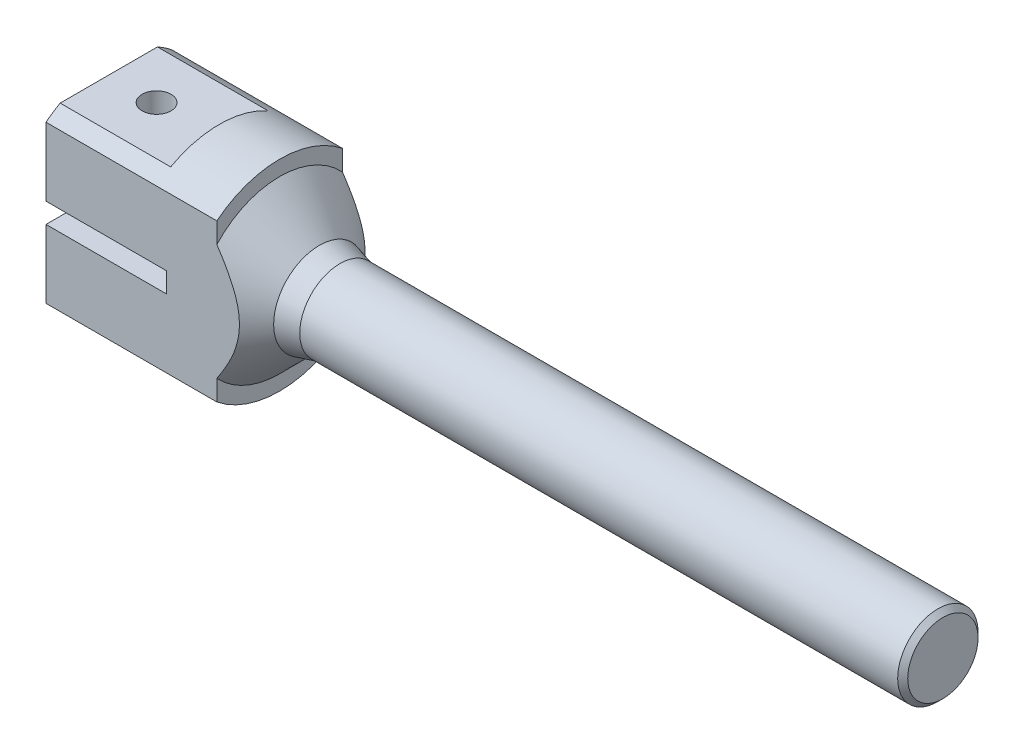
SolidWorks part; units mm, degrees
ref_plane "Ebene vorne" through (0, 0, 0) normal (0, 0, 1) x (1, 0, 0)
ref_plane "Ebene oben" through (0, 0, 0) normal (0, 1, 0) x (1, 0, 0)
ref_plane "Ebene rechts" through (0, 0, 0) normal (1, 0, 0) x (0, 0, -1)
sketch "Skizze1" plane through (0, 0, 0) normal (0, 0, 1) x (1, 0, 0)
  line L0 (0, 0) -> (0, 8)
  line L1 (-166, 20) -> (-132, 20)
  line L2 (0, 8) -> (-120, 8)
  line L3 (-120, 8) -> (-124.0981, 9.0981)
  line L4 (-132, 20) -> (-132, 17)
  line L7 (-166, 20) -> (-166, 0)
  line L8 (-166, 0) -> (0, 0)
  line L9 (0, 0) -> (10, 0) construction
  line L10 (-132, 17) -> (-124.0981, 9.0981)
  dimension "D1" = 10
  dimension "D2" = 16
  dimension "D3" = 40
  dimension "D5" = 166
  dimension "D7" = 34
  dimension "D8" = 34
  dimension "D9" = 135
  dimension "D10" = 120
  dimension "D11" = 15
revolve "Rotation1" add sketch "Skizze1" angle 360 about L9
cosmetic thread "Gewindedarstellung1" parameters "D1"=100, "D2"=14.344
sketch "Skizze2" plane through (0, 0, 0) normal (0, 0, 1) x (1, 0, 0)
  line L0 (0, 0) -> (-166, 0) construction
  line L1 (-166, 20) -> (-144, 20)
  line L2 (-166, 20) -> (-166, 17.5)
  line L3 (-166, 17.5) -> (-144, 17.5)
  line L4 (-144, 20) -> (-144, 17.5)
  line L5 (-166, 2) -> (-142, 2)
  line L6 (-166, 2) -> (-166, -2)
  line L7 (-166, -2) -> (-142, -2)
  line L8 (-142, 2) -> (-142, -2)
  line L9 (-166, -17.5) -> (-144, -17.5)
  line L10 (-166, -17.5) -> (-166, -20)
  line L11 (-166, -20) -> (-144, -20)
  line L12 (-144, -17.5) -> (-144, -20)
  line L13 (-166, 20) -> (-166, -20) construction
  line L14 (-132, 20) -> (-166, 20) construction
  line L15 (-166, -20) -> (-132, -20) construction
  dimension "D1" = 22
  dimension "D2" = 35
  dimension "D3" = 4
  dimension "D4" = 24
extrude "Schnitt-Linear austragen1" cut sketch "Skizze2" against normal mid plane 100
sketch "Skizze3" plane through (0, 17.5, 0) normal (0, 1, 0) x (1, 0, 0)
  line L0 (-156.5, 0) -> (-166, 0) construction
  line L1 (-166, -9.6825) -> (-166, 9.6825) construction
  line L2 (-142, -20) -> (-132, -20) construction
  line L3 (-166, -12.5) -> (-127.5, -12.5)
  line L4 (-166, -12.5) -> (-166, -20)
  line L5 (-166, -20) -> (-127.5, -20)
  line L6 (-127.5, -12.5) -> (-127.5, -20)
  line L7 (-166, 12.5) -> (-127.5, 12.5)
  line L8 (-166, 12.5) -> (-166, 20)
  line L9 (-166, 20) -> (-127.5, 20)
  line L10 (-127.5, 12.5) -> (-127.5, 20)
  line L12 (-132, 20) -> (-142, 20) construction
  line L13 (-132, -17) -> (-124.0981, -9.0981) construction
  circle A0 centre (-156.5, 0) radius 2.875
  dimension "D1" = 5.75
  dimension "D2" = 9.5
  dimension "D3" = 25
extrude "Schnitt-Linear austragen2" cut sketch "Skizze3" against normal through all
chamfer "Fase1" distance 1 angle 45 1 edges at (0, 0, 8)
